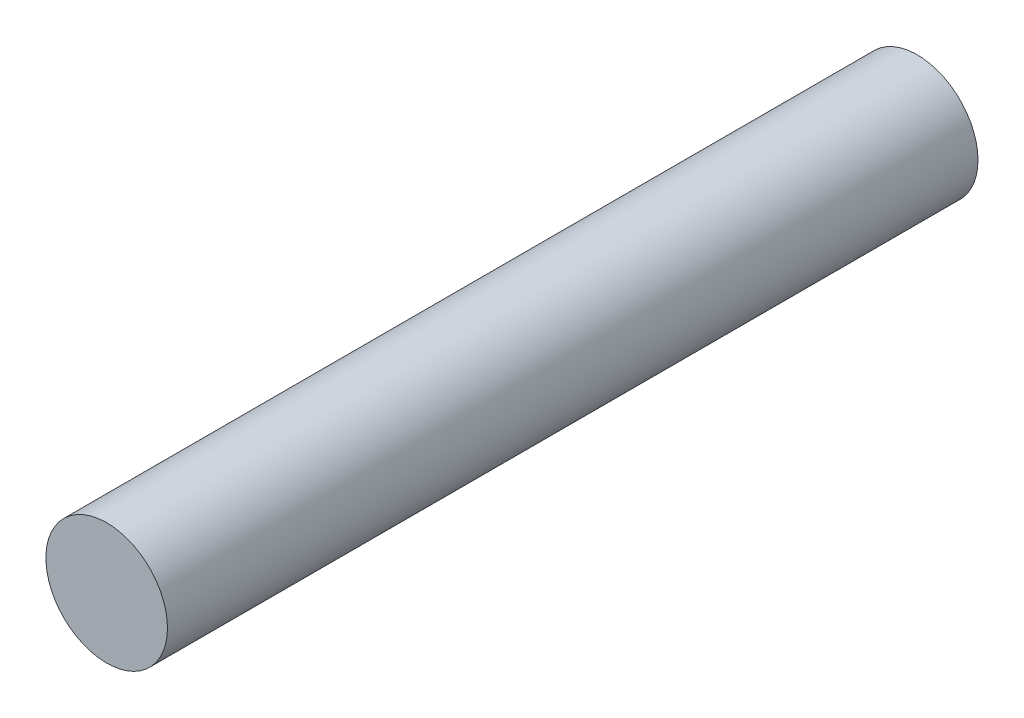
SolidWorks part; units mm, degrees
ref_plane "前基準面" through (0, 0, 0) normal (0, 0, 1) x (1, 0, 0)
ref_plane "上基準面" through (0, 0, 0) normal (0, 1, 0) x (1, 0, 0)
ref_plane "右基準面" through (0, 0, 0) normal (1, 0, 0) x (0, 0, -1)
sketch "草圖1" plane through (0, 0, 0) normal (0, 0, 1) x (1, 0, 0)
  circle A0 centre (0, 0) radius 1.5
  dimension "D1" = 3
extrude "填料-伸長1" add sketch "草圖1" along normal mid plane 20
